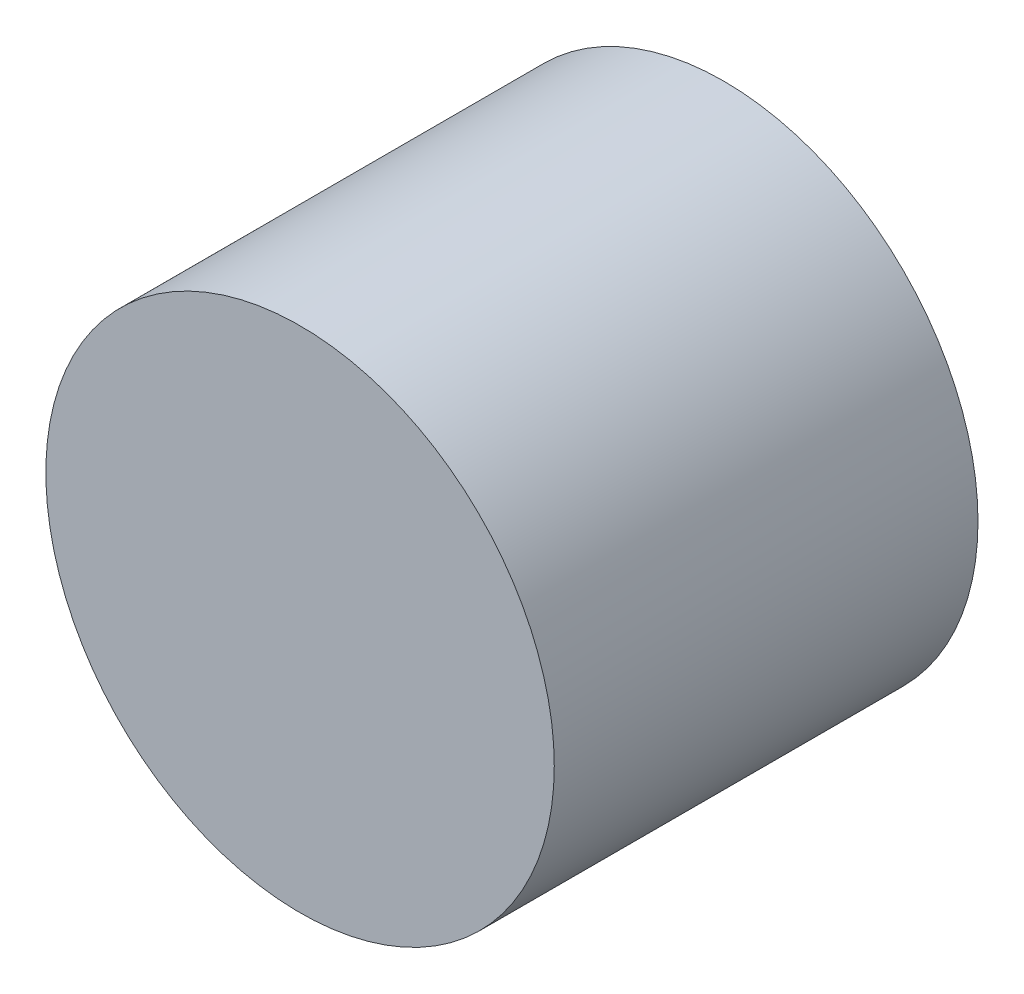
SolidWorks part; units mm, degrees
ref_plane "Front Plane" through (0, 0, 0) normal (0, 0, 1) x (1, 0, 0)
ref_plane "Top Plane" through (0, 0, 0) normal (0, 1, 0) x (1, 0, 0)
ref_plane "Right Plane" through (0, 0, 0) normal (1, 0, 0) x (0, 0, -1)
sketch "Sketch1" plane through (0, 0, 0) normal (0, 0, 1) x (1, 0, 0)
  circle A0 centre (15, 52.5) radius 6 construction
  circle A1 centre (15, 52.5) radius 6
extrude "Extrude2" add sketch "Sketch1" against normal offset from surface (10 mm away) 10
equation "\"D1@Extrude2\" = \"D1@Sketch1@busbar.sldprt\"+5"
